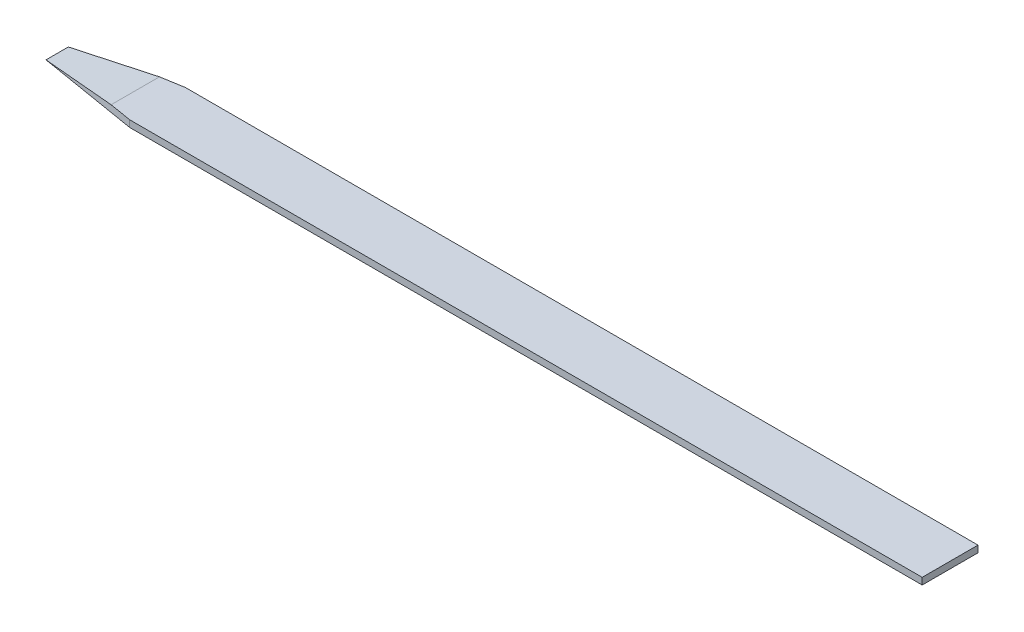
SolidWorks part; units mm, degrees
ref_plane "Front Plane" through (0, 0, 0) normal (0, 0, 1) x (1, 0, 0)
ref_plane "Top Plane" through (0, 0, 0) normal (0, 1, 0) x (1, 0, 0)
ref_plane "Right Plane" through (0, 0, 0) normal (1, 0, 0) x (0, 0, -1)
sketch "Sketch1" plane through (0, 0, 0) normal (0, 1, 0) x (1, 0, 0)
  line L0 (0, 1) -> (0, -1)
  line L1 (-8, -0.25) -> (0, -0.25)
  line L2 (-8, -0.25) -> (-8, 0.25)
  line L3 (0, -0.25) -> (0, 0.25)
  line L4 (-8, 0.25) -> (0, 0.25)
  line L5 (-8, -0.25) -> (0, 0.25) construction
  line L6 (0, -0.25) -> (-8, 0.25) construction
  line L7 (0, 1) -> (-4, 0.25)
  line L8 (0, -1) -> (-4, -0.25)
  line L9 (-4, -0.25) -> (-8, -0.25)
  line L10 (-8, 0.25) -> (-4, 0.25)
  arc A0 (0, 1) -> (0, -1) centre (0, 0) ccw
  point P4 (-1, 0)
  point P6 (-4, 0)
  dimension "D1" = 2
  dimension "D2" = 1
  dimension "D3" = 8
  dimension "D4" = 0.5
extrude "Boss-Extrude1" add sketch "Sketch1" along normal blind 0.06 contours A0 L1 L8 | A0 L7 L4 | A0 L4 L2 L1 | L1 A0 L8 L0 | L7 A0 L4 L0 | L4 A0 L1 L0
sketch "Sketch5" plane through (0, 0, 0.25) normal (0, 0, 1) x (1, 0, 0)
  line L0 (-8, 0) -> (-8, 0.06)
  line L1 (-8, 0.06) -> (-7.3, 0.06)
  line L2 (-8, 0.06) -> (-4, 0.06) construction
  line L3 (-7.3, 0.06) -> (-8, 0)
  dimension "D1" = 0.7
extrude "Cut-Extrude3" cut sketch "Sketch5" against normal through all contours L3 L0 L1
sketch3d "3DSketch1"
  line L0 (-7.3, 0.06, -0.25) -> (-7.3, 0.06, 0.25)
  line L4 (-8, 0.06, 0.25) -> (-8, 0.06, 0.1)
  line L8 (-8, 0.06, 0.1) -> (-7.1, 0.06, 0.25)
  line L9 (-7.1, 0.06, 0.25) -> (-8, 0.06, 0.25)
  line L11 (-7.3, 0.06, 0.25) -> (-4, 0.06, 0.25) construction
  line L13 (-8, 0, 0) -> (-7.2904, 0, 0) construction
  line L14 (-8, 0, 0.25) -> (-8, 0, -0.25) construction
  line L15 (-7.1, 0.06, -0.25) -> (-8, 0.06, -0.25)
  line L16 (-8, 0.06, -0.1) -> (-7.1, 0.06, -0.25)
  line L17 (-8, 0.06, -0.25) -> (-8, 0.06, -0.1)
  dimension "D1" = 0.15
  dimension "D2" = 0.7
  dimension "D3" = 0.9
  dimension "D4" = 0.2
extrude "Cut-Extrude4" cut sketch "3DSketch1" along direction (0, 1, 0) on the side of the normal through all contours L15 L17 L16 | L8 L9 L4
sketch "Sketch6" plane through (0, 0.06, 0) normal (0, 1, 0) x (1, 0, 0)
  line L0 (-7.1, 0.25) -> (-7.1, -0.25)
  line L1 (-7.1, -0.25) -> (0, -0.25)
  line L2 (0, 1) -> (0, -1) construction
  line L3 (0, -0.25) -> (0, 0.25)
  line L4 (0, 0.25) -> (-7.1, 0.25)
  line L5 (-4, 0.25) -> (0, 1)
  line L6 (0, 1) -> (0, 0.25)
  line L7 (0, -0.25) -> (0, -1)
  line L8 (0, -1) -> (-4, -0.25)
  line L9 (-4, -0.25) -> (0, -0.25)
  line L10 (-4, 0.25) -> (0, 0.25)
  line M10 (-4, -0.25) -> (0, -1)
  line M11 (0, -1) -> (0, 1)
  line M12 (0, 1) -> (-4, 0.25)
extrude "Cut-Extrude5" cut sketch "Sketch6" against normal blind 2.5 contours L4 M11 M12 | L1 M10 M11
